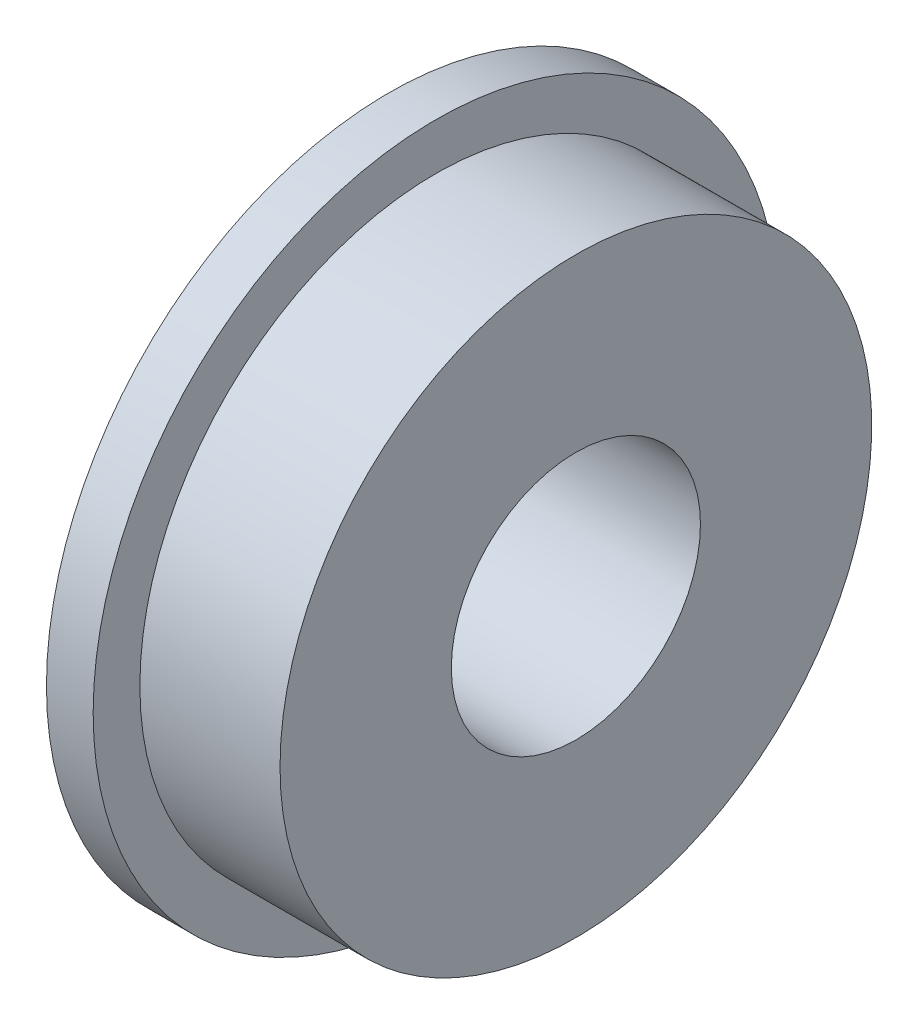
SolidWorks part; units mm, degrees
ref_plane "Front" through (0, 0, 0) normal (0, 0, 1) x (1, 0, 0)
ref_plane "Top" through (0, 0, 0) normal (0, 1, 0) x (1, 0, 0)
ref_plane "Right" through (0, 0, 0) normal (1, 0, 0) x (0, 0, -1)
ref_plane "Plane1" through (0, 0, 0) normal (0, 0, -1) x (-1, 0, 0)
sketch "Sketch1" plane through (0, 0, 0) normal (0, 0, -1) x (-1, 0, 0)
  line L0 (-1.5, 9.5) -> (-6, 9.5)
  line L1 (-6, 9.5) -> (-6, 4)
  line L2 (-6, 4) -> (0, 4)
  line L3 (0, 4) -> (0, 11)
  line L4 (0, 11) -> (-1.5, 11)
  line L5 (-1.5, 11) -> (-1.5, 9.5)
  line L6 (-6, 0) -> (0, 0) construction
revolve "Revolve1" add sketch "Sketch1" angle 360 about L6
